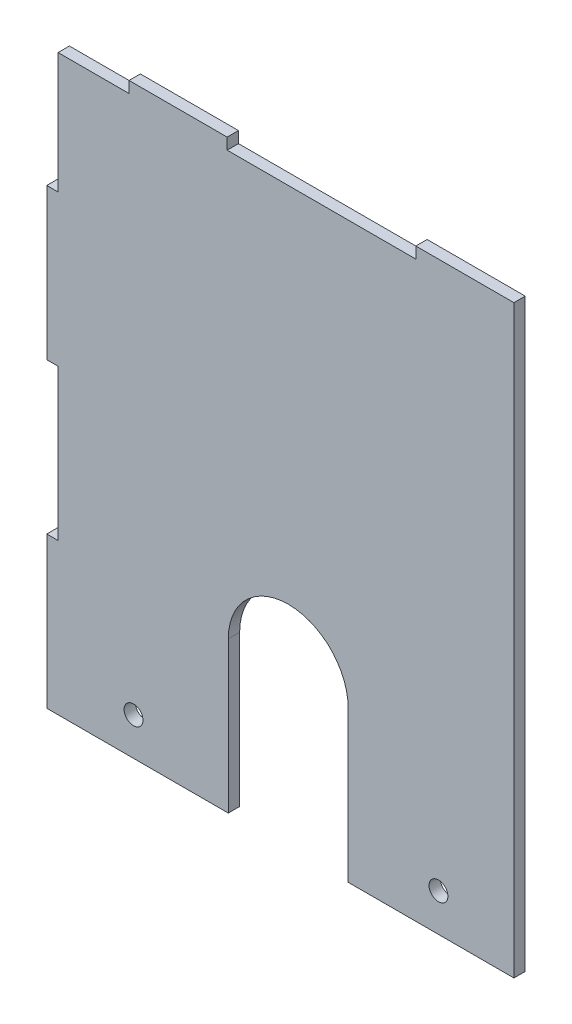
SolidWorks part; units mm, degrees
ref_plane "Front Plane" through (0, 0, 0) normal (0, 0, 1) x (1, 0, 0)
ref_plane "Top Plane" through (0, 0, 0) normal (0, 1, 0) x (1, 0, 0)
ref_plane "Right Plane" through (0, 0, 0) normal (1, 0, 0) x (0, 0, -1)
sketch "Sketch1" plane through (0, 0, 0) normal (0, 0, 1) x (1, 0, 0)
  line L1 (34.37, 75.956) -> (-15.63, 75.956)
  line L2 (60.37, 75.956) -> (60.37, -76.044)
  line L3 (60.37, -76.044) -> (16.4443, -76.044)
  line L4 (-60.44, 3.956) -> (-60.44, -36.044)
  line L5 (60.37, 75.956) -> (-60.44, -76.044) construction
  line L6 (60.37, -76.044) -> (0, 0) construction
  line L7 (-15.3243, -36.044) -> (-15.3243, -76.044)
  line L8 (16.4443, -36.044) -> (16.4443, -76.044)
  line L9 (-15.3243, -76.044) -> (-60.44, -76.044)
  line L10 (-41.63, 75.956) -> (-41.63, 78.956)
  line L11 (-41.63, 78.956) -> (-15.63, 78.956)
  line L12 (-15.63, 78.956) -> (-15.63, 75.956)
  line L13 (60.37, 75.956) -> (60.37, 78.956)
  line L14 (60.37, 78.956) -> (34.37, 78.956)
  line L15 (34.37, 78.956) -> (34.37, 75.956)
  line L16 (-60.44, 43.956) -> (-63.44, 43.956)
  line L17 (-63.44, 43.956) -> (-63.44, 3.956)
  line L18 (-63.44, 3.956) -> (-60.44, 3.956)
  line L19 (-60.44, -76.044) -> (-63.44, -76.044)
  line L20 (-63.44, -76.044) -> (-63.44, -36.044)
  line L21 (-63.44, -36.044) -> (-60.44, -36.044)
  line L30 (-41.63, 75.956) -> (-60.44, 75.956)
  line L31 (-60.44, 75.956) -> (-60.44, 43.956)
  circle A0 centre (-40.44, -66.044) radius 2.5
  circle A1 centre (40.37, -66.044) radius 2.5
  arc A2 (16.4443, -36.044) -> (-15.3243, -36.044) centre (0.56, -36.044) ccw
  point P0 (0, 0)
  dimension "D6" = 5
  dimension "D7" = 20
  dimension "D8" = 10
  dimension "D9" = 5
  dimension "D10" = 10
  dimension "D11" = 20
  dimension "D12" = 40
  dimension "D13" = 61
  dimension "D1" = 120.81
  dimension "D2" = 152
  dimension "D3" = 102
  dimension "D4" = 120
  dimension "D5" = 60.44
  dimension "D14" = 50
  dimension "D15" = 26
  dimension "D16" = 3
  dimension "D17" = 3
  dimension "D18" = 40
  dimension "D19" = 40
  dimension "D20" = 3
extrude "Boss-Extrude1" add sketch "Sketch1" along normal blind 3
